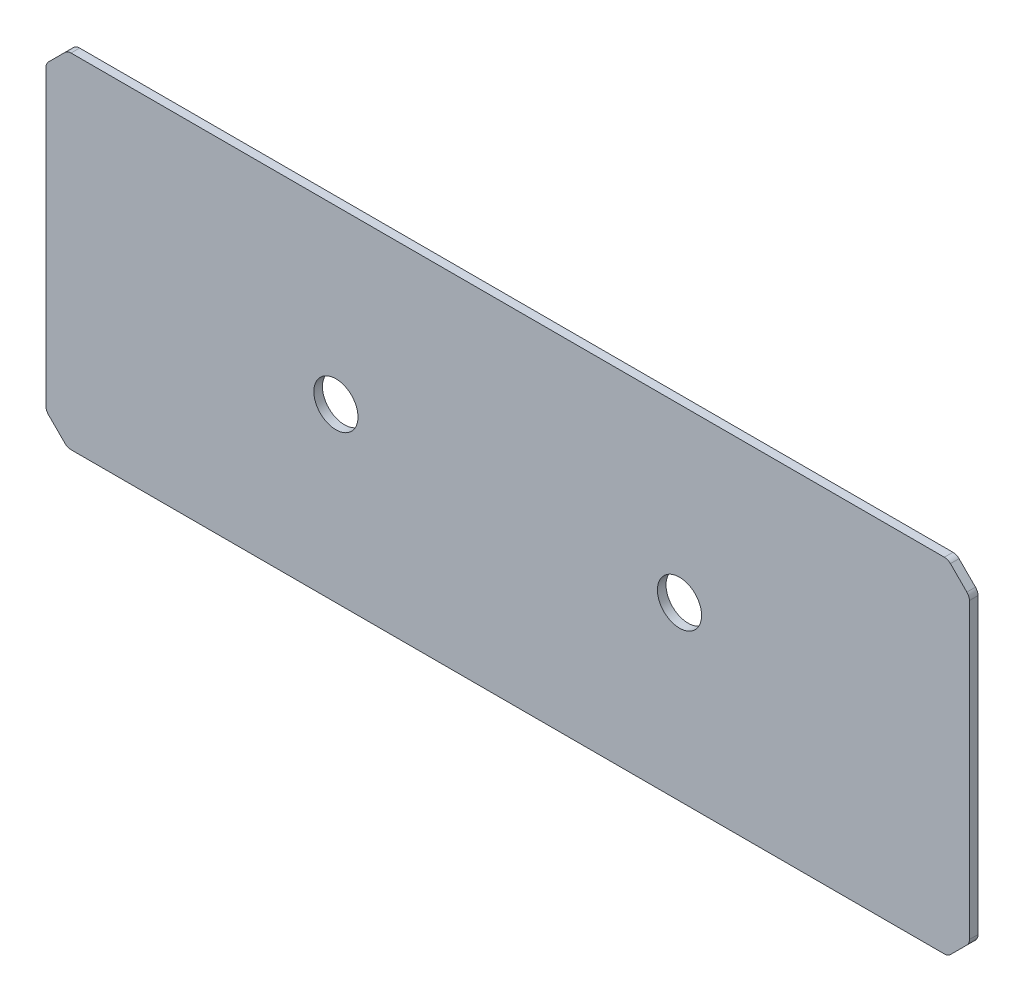
SolidWorks part; units mm, degrees
ref_plane "Front" through (0, 0, 0) normal (0, 0, 1) x (1, 0, 0)
ref_plane "Top" through (0, 0, 0) normal (0, 1, 0) x (1, 0, 0)
ref_plane "Right" through (0, 0, 0) normal (1, 0, 0) x (0, 0, -1)
sketch "Sketch1" plane through (0, 0, 0) normal (0, 0, 1) x (1, 0, 0)
  line L1 (0, 0) -> (136.525, 0)
  line L2 (0, 0) -> (0, 50.8)
  line L3 (0, 50.8) -> (136.525, 50.8)
  line L4 (136.525, 0) -> (136.525, 50.8)
  dimension "D1" = 50.8
  dimension "D2" = 136.525
extrude "Boss-Extrude1" add sketch "Sketch1" along normal blind 1.27 contours L1 L4 L3 L2
sketch "Sketch3" plane through (0, 0, 1.27) normal (0, 0, 1) x (1, 0, 0)
  line L1 (136.525, 0) -> (136.525, 50.8) construction
  line L2 (0, 50.8) -> (136.525, 50.8) construction
  circle A0 centre (42.8625, 25.4) radius 3.2639
  circle A1 centre (93.6625, 25.4) radius 3.2639
  dimension "D1" = 6.5278
  dimension "D2" = 6.5278
  dimension "D3" = 50.8
  dimension "D4" = 42.8625
  dimension "D5" = 25.4
  dimension "D6" = 25.4
extrude "Cut-Extrude1" cut sketch "Sketch3" against normal through all contours A1 | A0
chamfer "Chamfer1" distance 3.175 angle 45 4 edges at (0, 0, 0.635) (0, 50.8, 0.635) (136.525, 50.8, 0.635) (136.525, 0, 0.635)
fillet "Fillet1" radius 1.27 8 edges at (0, 47.625, 0.635) (3.175, 50.8, 0.635) (133.35, 50.8, 0.635) (136.525, 47.625, 0.635) (136.525, 3.175, 0.635) (133.35, 0, 0.635) (3.175, 0, 0.635) (0, 3.175, 0.635)
